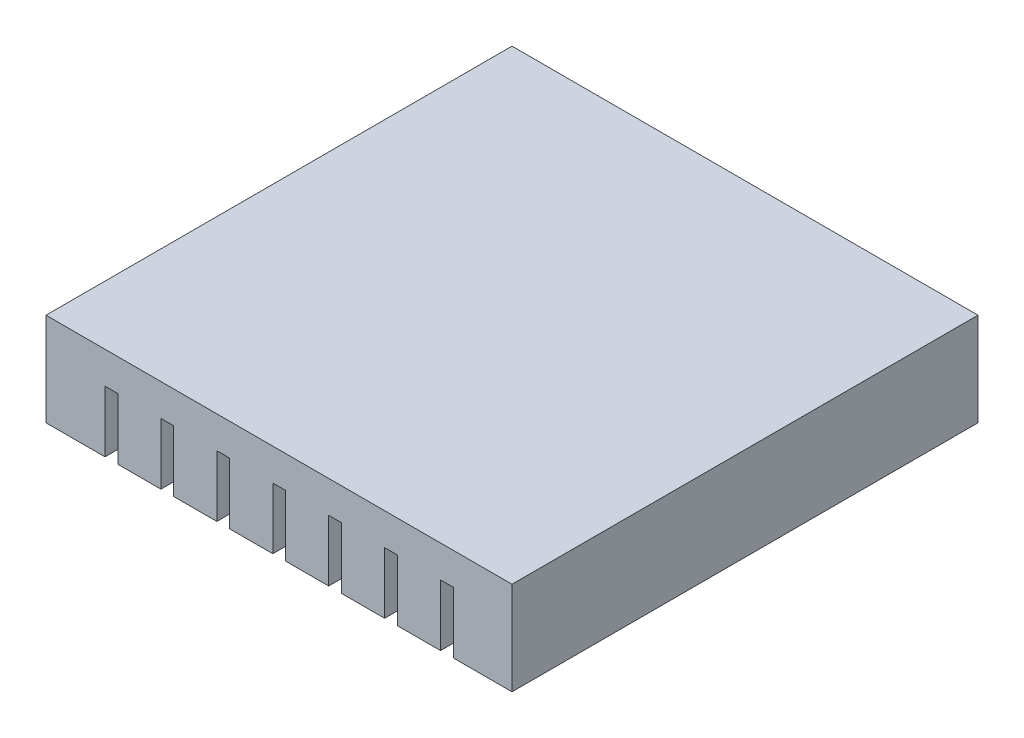
SolidWorks part; units mm, degrees
ref_plane "Front Plane" through (0, 0, 0) normal (0, 0, 1) x (1, 0, 0)
ref_plane "Top Plane" through (0, 0, 0) normal (0, 1, 0) x (1, 0, 0)
ref_plane "Right Plane" through (0, 0, 0) normal (1, 0, 0) x (0, 0, -1)
sketch "Sketch1" plane through (0, 0, 0) normal (0, 1, 0) x (1, 0, 0)
  line L1 (0, 0) -> (50, 0)
  line L2 (0, 0) -> (0, -50)
  line L3 (0, -50) -> (50, -50)
  line L4 (50, 0) -> (50, -50)
  dimension "D1" = 50
  dimension "D2" = 50
extrude "Boss-Extrude1" add sketch "Sketch1" along normal blind 10
sketch "Sketch3" plane through (0, 0, 50) normal (0, 0, 1) x (1, 0, 0)
  line L0 (0, 0) -> (50, 0) construction
  line L6 (6.331, 0) -> (7.701, 0)
  line L7 (6.331, 0) -> (6.331, 6.5688)
  line L8 (6.331, 6.5688) -> (7.701, 6.5688)
  line L9 (7.701, 0) -> (7.701, 6.5688)
  dimension "D2" = 1.37
extrude "Cut-Extrude1" cut sketch "Sketch3" against normal up to surface (50 mm away) up to face at (25, 5, 0)
pattern_linear "LPattern1" count 7 spacing 6 along (1, 0, 0) of "Cut-Extrude1"
